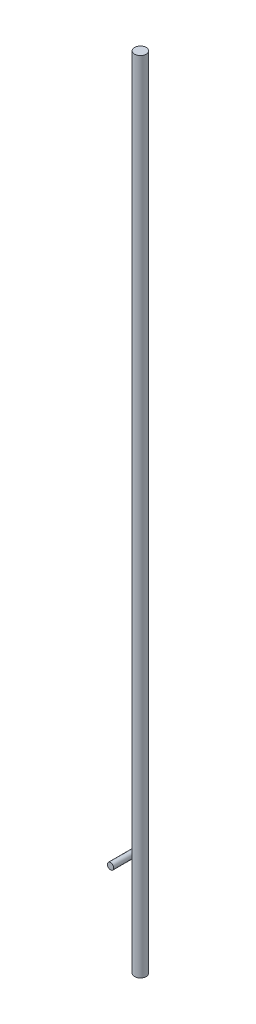
SolidWorks part; units mm, degrees
material "Chrome Stainless Steel"
ref_plane "Front Plane" through (0, 0, 0) normal (0, 0, 1) x (1, 0, 0)
ref_plane "Top Plane" through (0, 0, 0) normal (0, 1, 0) x (1, 0, 0)
ref_plane "Right Plane" through (0, 0, 0) normal (1, 0, 0) x (0, 0, -1)
sketch "Sketch1" plane through (0, 0, 0) normal (0, 1, 0) x (1, 0, 0)
  circle A0 centre (0, 0) radius 0.55
  dimension "D1" = 1.1
extrude "Extrude1" add sketch "Sketch1" along normal blind 66 and the other way blind 9
sketch "Sketch2" plane through (0, 0, 0) normal (0, 0, 1) x (1, 0, 0)
  line L0 (0.605, 0) -> (-0.605, 0) construction
  line L1 (0, -0.605) -> (0, 0.605) construction
  circle A0 centre (-0.8, 0.3) radius 0.3
  dimension "D1" = 0.6
  dimension "D2" = 0.3
  dimension "D3" = 0.8
extrude "Extrude2" add sketch "Sketch2" along normal blind 2 and the other way blind 0.5
